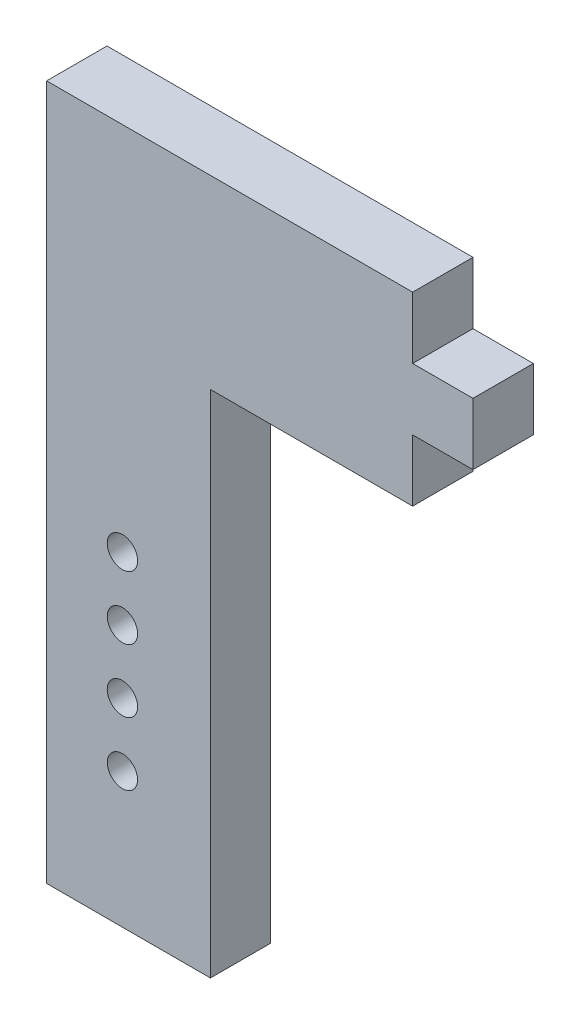
SolidWorks part; units mm, degrees
ref_plane "Front Plane" through (0, 0, 0) normal (0, 0, 1) x (1, 0, 0)
ref_plane "Top Plane" through (0, 0, 0) normal (0, 1, 0) x (1, 0, 0)
ref_plane "Right Plane" through (0, 0, 0) normal (1, 0, 0) x (0, 0, -1)
sketch "Sketch1" plane through (0, 0, 0) normal (0, 0, 1) x (1, 0, 0)
  line L1 (-6.731, 28.575) -> (6.731, 28.575)
  line L2 (-6.731, 28.575) -> (-6.731, -28.575)
  line L3 (-6.731, -28.575) -> (6.731, -28.575)
  line L4 (6.731, 28.575) -> (6.731, -28.575)
  line L5 (-6.731, 28.575) -> (6.731, -28.575) construction
  line L6 (-6.731, -28.575) -> (6.731, 28.575) construction
  point P0 (0, 0)
  dimension "D1" = 13.462
  dimension "D2" = 57.15
extrude "Boss-Extrude1" add sketch "Sketch1" along normal blind 4.9609
sketch "Sketch2" plane through (6.731, 0, 0) normal (1, 0, 0) x (0, 0, -1)
  line L0 (0, -28.575) -> (0, 28.575) construction
  line L1 (-4.9609, 28.575) -> (0, 28.575)
  line L2 (-4.9609, 28.575) -> (-4.9609, 13.335)
  line L3 (-4.9609, 13.335) -> (0, 13.335)
  line L4 (0, 28.575) -> (0, 13.335)
  dimension "D1" = 15.24
extrude "Boss-Extrude2" add sketch "Sketch2" along normal blind 21.59
sketch "Sketch5" plane through (0, 0, 0) normal (0, 0, -1) x (-1, 0, 0)
  line L0 (0.5022, -17.4625) -> (0.5022, -28.575) construction
  line L1 (0.5022, -17.4625) -> (0.5022, -12.2625) construction
  line L3 (6.731, -28.575) -> (-6.731, -28.575) construction
  line L4 (0.5022, -28.575) -> (0, -28.575) construction
  line L5 (0.5022, -12.2625) -> (0.5022, -7.0625) construction
  line L6 (0.5022, -7.0625) -> (0.5022, -1.8625) construction
  circle A0 centre (0.5022, -17.4625) radius 1.2446
  circle A4 centre (0.5022, -12.2625) radius 1.25
  circle A5 centre (0.5022, -7.0625) radius 1.2497
  circle A6 centre (0.5022, -1.8625) radius 1.2497
  dimension "D2" = 2.4892
  dimension "D4" = 2.5
  dimension "D7" = 2.4994
  dimension "D1" = 11.1125
  dimension "D5" = 0.5022
  dimension "D3" = 5.2
  dimension "D6" = 5.2
  dimension "D8" = 5.2
extrude "Cut-Extrude2" cut sketch "Sketch5" against normal through all
sketch "Sketch6" plane through (28.321, 0, 0) normal (1, 0, 0) x (0, 0, -1)
  line L0 (-4.9609, 28.575) -> (0, 13.335) construction
  line L1 (-4.9609, 13.335) -> (0, 28.575) construction
  line L2 (0, 13.335) -> (0, 28.575) construction
  line L3 (-4.9609, 23.495) -> (0, 23.495)
  line L4 (-4.9609, 23.495) -> (-4.9609, 18.415)
  line L5 (-4.9609, 18.415) -> (0, 18.415)
  line L6 (0, 23.495) -> (0, 18.415)
  line L7 (-4.9609, 23.495) -> (0, 18.415) construction
  line L8 (-4.9609, 18.415) -> (0, 23.495) construction
  point P8 (-2.4805, 20.955)
  dimension "D1" = 5.08
extrude "Cut-Extrude3" cut sketch "Sketch6" against normal blind 4.9609 flip side to cut
